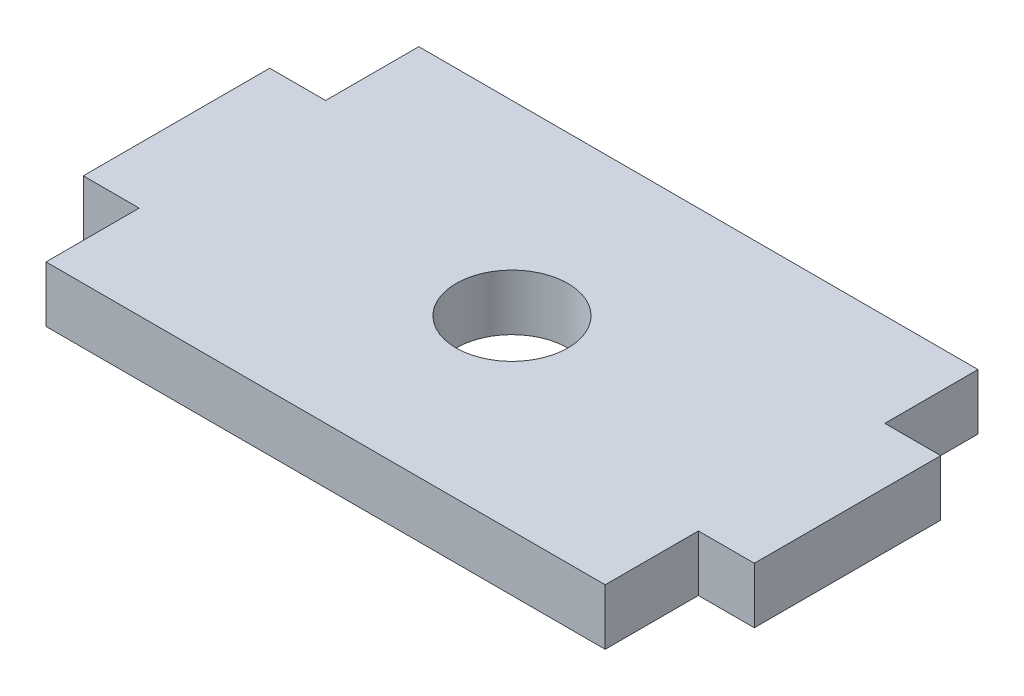
SolidWorks part; units mm, degrees
ref_plane "Front Plane" through (0, 0, 0) normal (0, 0, 1) x (1, 0, 0)
ref_plane "Top Plane" through (0, 0, 0) normal (0, 1, 0) x (1, 0, 0)
ref_plane "Right Plane" through (0, 0, 0) normal (1, 0, 0) x (0, 0, -1)
sketch "Sketch1" plane through (0, 0, 0) normal (0, 1, 0) x (1, 0, 0)
  line L0 (-15, 10) -> (-15, 5)
  line L1 (15, 10) -> (-15, 10)
  line L2 (-15, 5) -> (-18, 5)
  line L3 (15, -10) -> (-15, -10)
  line L4 (-18, 5) -> (-18, -5)
  line L5 (15, 10) -> (-15, -10) construction
  line L6 (15, -10) -> (-15, 10) construction
  line L7 (-18, -5) -> (-15, -5)
  line L8 (-15, -5) -> (-15, -10)
  line L9 (15, -10) -> (15, -5)
  line L10 (15, -5) -> (18, -5)
  line L11 (18, -5) -> (18, 5)
  line L12 (18, 5) -> (15, 5)
  line L13 (15, 5) -> (15, 10)
  circle A0 centre (0, 0) radius 3
  point P0 (0, 0)
  dimension "D5" = 6
  dimension "D1" = 30
  dimension "D2" = 20
  dimension "D3" = 5
  dimension "D4" = 3
extrude "Boss-Extrude1" add sketch "Sketch1" along normal blind 3
